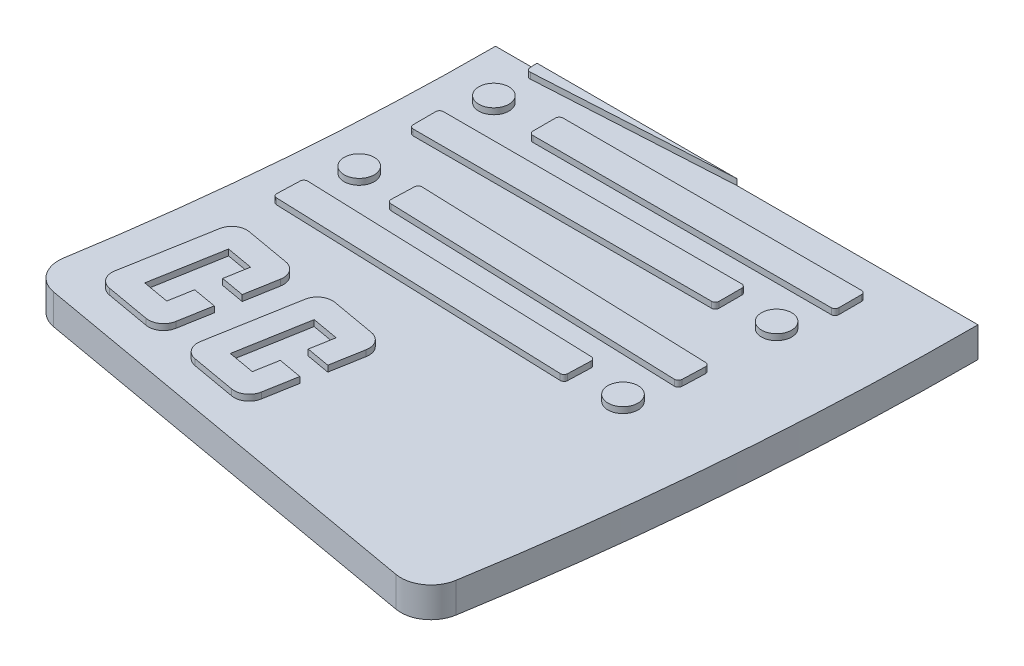
SolidWorks part; units mm, degrees
material "6061-T4 (SS)"
ref_plane "Front" through (0, 0, 0) normal (0, 0, 1) x (1, 0, 0)
ref_plane "Top" through (0, 0, 0) normal (0, 1, 0) x (1, 0, 0)
ref_plane "Right" through (0, 0, 0) normal (1, 0, 0) x (0, 0, -1)
sketch "Sketch1" plane through (0, 0, 0) normal (0, 1, 0) x (1, 0, 0)
  line L0 (-101.6, 0) -> (101.6, 0)
  line L1 (-117.4153, -180.5061) -> (82.6886, -215.8422)
  line L2 (-101.6, 0) -> (-101.6, 83.31) construction
  arc A0 (-101.6, 0) -> (-117.4153, -180.5061) centre (-1139.598, 0) cw
  arc A1 (82.6886, -215.8422) -> (101.6, 0) centre (-1139.598, 0) ccw
  dimension "D1" = 203.2
extrude "Boss-Extrude1" add sketch "Sketch1" along normal blind 12.7
fillet "Fillet1" radius 12.7 2 edges at (82.6886, 6.35, 215.8422) (-117.4153, 6.35, 180.5061)
sketch "Sketch2" plane through (0, 12.7, 0) normal (0, 1, 0) x (1, 0, 0)
  line L12 (-54.6146, -178.6995) -> (-23.3484, -184.2208)
  line L13 (-84.9628, -186.2369) -> (-82.7543, -173.7304) construction
  line L14 (-104.9844, -182.7012) -> (70.1175, -213.6223) construction
  line L15 (-98.3874, -170.9697) -> (-67.1211, -176.491)
  line L16 (-98.3874, -170.9697) -> (-89.5533, -120.9437)
  line L17 (-89.5533, -120.9437) -> (-58.2871, -126.465)
  line L18 (-58.2871, -126.465) -> (-61.8207, -146.4754)
  line L19 (-61.8207, -146.4754) -> (-71.8259, -144.7086)
  line L20 (-71.8259, -144.7086) -> (-70.0591, -134.7034)
  line L21 (-70.0591, -134.7034) -> (-81.315, -132.7157)
  line L22 (-81.315, -132.7157) -> (-86.6154, -162.7313)
  line L23 (-86.6154, -162.7313) -> (-75.3595, -164.719)
  line L24 (-75.3595, -164.719) -> (-73.5927, -154.7138)
  line L25 (-73.5927, -154.7138) -> (-63.5875, -156.4806)
  line L26 (-63.5875, -156.4806) -> (-67.1211, -176.491)
  line L27 (-82.7543, -173.7304) -> (-80.9874, -163.7252) construction
  line L28 (-83.9652, -147.7235) -> (-93.9704, -145.9567) construction
  line L29 (-54.6146, -178.6995) -> (-45.7806, -128.6735)
  line L30 (-45.7806, -128.6735) -> (-14.5144, -134.1948)
  line L31 (-14.5144, -134.1948) -> (-18.048, -154.2052)
  line L32 (-18.048, -154.2052) -> (-28.0532, -152.4384)
  line L33 (-28.0532, -152.4384) -> (-26.2864, -142.4332)
  line L34 (-26.2864, -142.4332) -> (-37.5422, -140.4455)
  line L35 (-37.5422, -140.4455) -> (-42.8426, -170.4611)
  line L36 (-42.8426, -170.4611) -> (-31.5868, -172.4488)
  line L37 (-31.5868, -172.4488) -> (-29.82, -162.4436)
  line L38 (-29.82, -162.4436) -> (-19.8148, -164.2104)
  line L39 (-19.8148, -164.2104) -> (-23.3484, -184.2208)
  line L40 (-38.9815, -181.4601) -> (-37.2147, -171.4549) construction
  line L41 (-40.1924, -155.4533) -> (-50.1976, -153.6865) construction
  point P7 (-82.7543, -173.7304)
  point P33 (-38.9815, -181.4601)
  dimension "D1" = 10.16
  dimension "D2" = 10.16
  dimension "D3" = 12.7
  dimension "D4" = 50.8
  dimension "D5" = 31.75
  dimension "D6" = 33.0309
  dimension "D7" = 10.16
  dimension "D8" = 12.7
extrude "Boss-Extrude2" add sketch "Sketch2" along normal blind 2.54
fillet "Fillet2" radius 6.35 8 edges at (-54.6146, 13.97, 178.6995) (-23.3484, 13.97, 184.2208) (-14.5144, 13.97, 134.1948) (-45.7806, 13.97, 128.6735) (-67.1211, 13.97, 176.491) (-98.3874, 13.97, 170.9697) (-89.5533, 13.97, 120.9437) (-58.2871, 13.97, 126.465)
sketch "Sketch3" plane through (0, 12.7, 0) normal (0, 1, 0) x (1, 0, 0)
  line L0 (-84.0615, -74.9557) -> (-1.5618, -77.8367) construction
  line L1 (-65.2447, -81.9667) -> (61.6779, -86.3989)
  line L2 (-65.2447, -81.9667) -> (-64.8015, -69.2744)
  line L3 (61.6779, -86.3989) -> (62.1212, -73.7067)
  line L4 (-64.8015, -69.2744) -> (62.1212, -73.7067)
  line L5 (-65.2447, -81.9667) -> (62.1212, -73.7067) construction
  line L6 (61.6779, -86.3989) -> (-64.8015, -69.2744) construction
  line L7 (101.6, 0) -> (-101.6, 0) construction
  line L8 (-91.427, -103.9263) -> (35.4956, -108.3586)
  line L9 (-91.427, -103.9263) -> (-90.9838, -91.2341)
  line L10 (35.4956, -108.3586) -> (35.9388, -95.6663)
  line L11 (-90.9838, -91.2341) -> (35.9388, -95.6663)
  line L12 (-91.427, -103.9263) -> (35.9388, -95.6663) construction
  line L13 (35.4956, -108.3586) -> (-90.9838, -91.2341) construction
  line L14 (54.7556, -102.6773) -> (35.7172, -102.0124) construction
  line L15 (-81.4434, -20.8685) -> (4.1802, -20.8685) construction
  line L16 (-60.2412, -27.2185) -> (68.6015, -27.2185)
  line L17 (-60.2412, -27.2185) -> (-60.2412, -14.5185)
  line L18 (68.6015, -27.2185) -> (68.6015, -14.5185)
  line L19 (-60.2412, -14.5185) -> (68.6015, -14.5185)
  line L20 (-60.2412, -27.2185) -> (68.6015, -14.5185) construction
  line L21 (68.6015, -27.2185) -> (-60.2412, -14.5185) construction
  line L22 (-87.7934, -50.0785) -> (41.0493, -50.0785)
  line L23 (-87.7934, -50.0785) -> (-87.7934, -37.3785)
  line L24 (41.0493, -50.0785) -> (41.0493, -37.3785)
  line L25 (-87.7934, -37.3785) -> (41.0493, -37.3785)
  line L26 (-87.7934, -50.0785) -> (41.0493, -37.3785) construction
  line L27 (41.0493, -50.0785) -> (-87.7934, -37.3785) construction
  line L28 (60.4958, -43.7285) -> (41.0493, -43.7285) construction
  line L29 (-84.1538, 0) -> (-83.8826, -4.7697)
  line L30 (-83.8826, -4.7697) -> (0, 0)
  line L31 (-84.1538, 0) -> (0, 0)
  circle A0 centre (-84.0615, -74.9557) radius 6.35
  circle A1 centre (54.7556, -102.6773) radius 6.35
  circle A2 centre (-81.4434, -20.8685) radius 6.35
  circle A3 centre (60.4958, -43.7285) radius 6.35
  point P15 (-27.7441, -99.7963)
  point P29 (-23.3721, -43.7285)
  dimension "D1" = 127
  dimension "D2" = 12.7
  dimension "D3" = 19.05
  dimension "D4" = 2
  dimension "D5" = 19.05
  dimension "D6" = 10.16
  dimension "D7" = 12.7
  dimension "D8" = 10.16
extrude "Boss-Extrude3" add sketch "Sketch3" along normal blind 2.54
fillet "Fillet3" radius 1.5875 17 edges at (-65.2447, 13.97, 81.9667) (61.6779, 13.97, 86.3989) (-64.8015, 13.97, 69.2744) (62.1212, 13.97, 73.7067) (-91.427, 13.97, 103.9263) (35.4956, 13.97, 108.3586) (-90.9838, 13.97, 91.2341) (35.9388, 13.97, 95.6663) (-83.8826, 13.97, 4.7697) (68.6015, 13.97, 27.2185) (68.6015, 13.97, 14.5185) (-60.2412, 13.97, 14.5185) (-60.2412, 13.97, 27.2185) (-87.7934, 13.97, 50.0785) (41.0493, 13.97, 50.0785) (41.0493, 13.97, 37.3785) (-87.7934, 13.97, 37.3785)
equation "\"D5@Sketch3\"=\"D3@Sketch3\""
